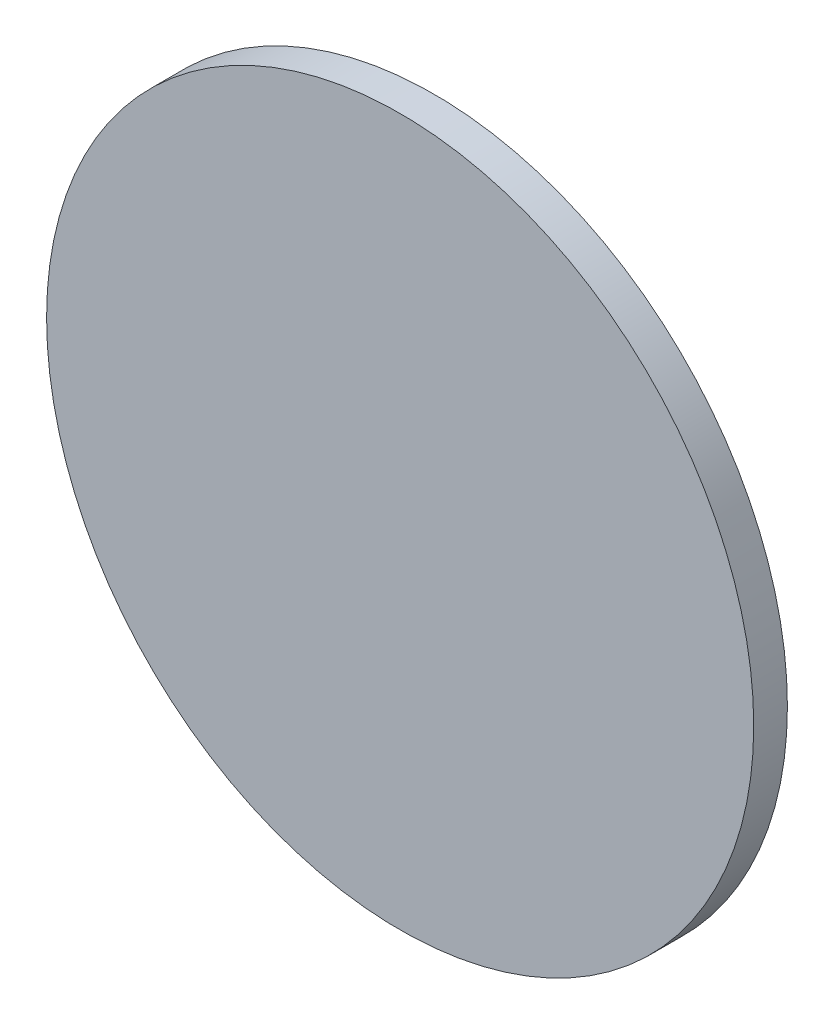
SolidWorks part; units mm, degrees
ref_plane "Plan de face" through (0, 0, 0) normal (0, 0, 1) x (1, 0, 0)
ref_plane "Plan de dessus" through (0, 0, 0) normal (0, 1, 0) x (1, 0, 0)
ref_plane "Plan de droite" through (0, 0, 0) normal (1, 0, 0) x (0, 0, -1)
sketch "Esquisse1" plane through (0, 0, 0) normal (0, 0, 1) x (1, 0, 0)
  circle A0 centre (0, 0) radius 42
  dimension "D1" = 84
extrude "Boss.-Extru.1" add sketch "Esquisse1" along normal blind 4
